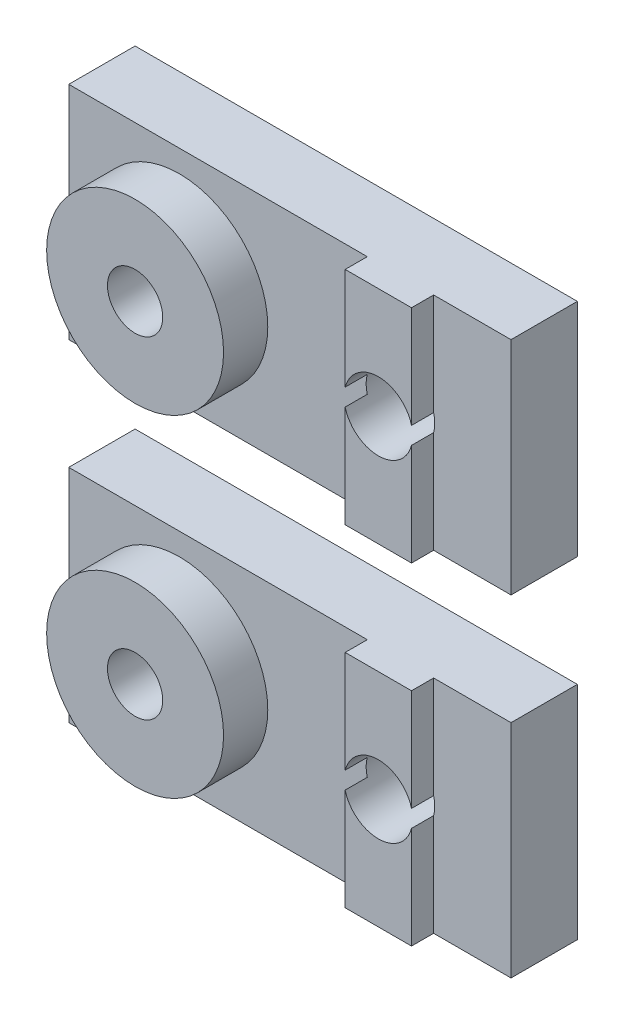
SolidWorks part; units mm, degrees
ref_plane "Front Plane" through (0, 0, 0) normal (0, 0, 1) x (1, 0, 0)
ref_plane "Top Plane" through (0, 0, 0) normal (0, 1, 0) x (1, 0, 0)
ref_plane "Right Plane" through (0, 0, 0) normal (1, 0, 0) x (0, 0, -1)
sketch "Sketch1" plane through (0, 0, 0) normal (0, 0, 1) x (1, 0, 0)
  line L1 (-10, 10) -> (10, 10)
  line L2 (-10, 10) -> (-10, 0)
  line L3 (-10, 0) -> (10, 0)
  line L4 (10, 10) -> (10, 0)
  point P4 (0, 0)
  point P5 (0, 0)
  dimension "D1" = 10
  dimension "D2" = 20
extrude "Boss-Extrude1" add sketch "Sketch1" along normal blind 3
sketch "Sketch2" plane through (0, 0, 3) normal (0, 0, 1) x (1, 0, 0)
  line L0 (-10, 10) -> (-10, 0) construction
  circle A0 centre (-5, 5) radius 4
  circle A1 centre (-5, 5) radius 1.25
  point P5 (-10, 5)
  point P6 (0, 0)
  dimension "D1" = 2.5
  dimension "D2" = 8
  dimension "D3" = 5
extrude "Boss-Extrude2" add sketch "Sketch2" along normal blind 2
sketch "Sketch3" plane through (0, 0, 3) normal (0, 0, 1) x (1, 0, 0)
  line L0 (-10, 0) -> (10, 0) construction
  line L1 (3.5, 10) -> (6.5, 10)
  line L2 (3.5, 10) -> (3.5, 0)
  line L3 (3.5, 0) -> (6.5, 0)
  line L4 (6.5, 10) -> (6.5, 0)
  line L5 (10, 10) -> (-10, 10) construction
  line L7 (10, 0) -> (10, 10) construction
  point P6 (4.5071, 10)
  dimension "D1" = 3
  dimension "D2" = 3.5
extrude "Boss-Extrude3" add sketch "Sketch3" along normal blind 1
sketch "Sketch4" plane through (0, 0, 0) normal (0, 0, 1) x (1, 0, 0)
  line L0 (10, 0) -> (10, 10) construction
  circle A0 centre (-5, 5) radius 1.25
  circle A1 centre (-5, 5) radius 1.25 construction
  circle A2 centre (5, 5) radius 1.55
  point P8 (10, 5)
  point P9 (0, 0)
  dimension "D1" = 5
  dimension "D2" = 3.1
extrude "Cut-Extrude1" cut sketch "Sketch4" along normal through all
pattern_linear "LPattern1" count 2 spacing 15 along (0, 1, 0) of bodies 104
